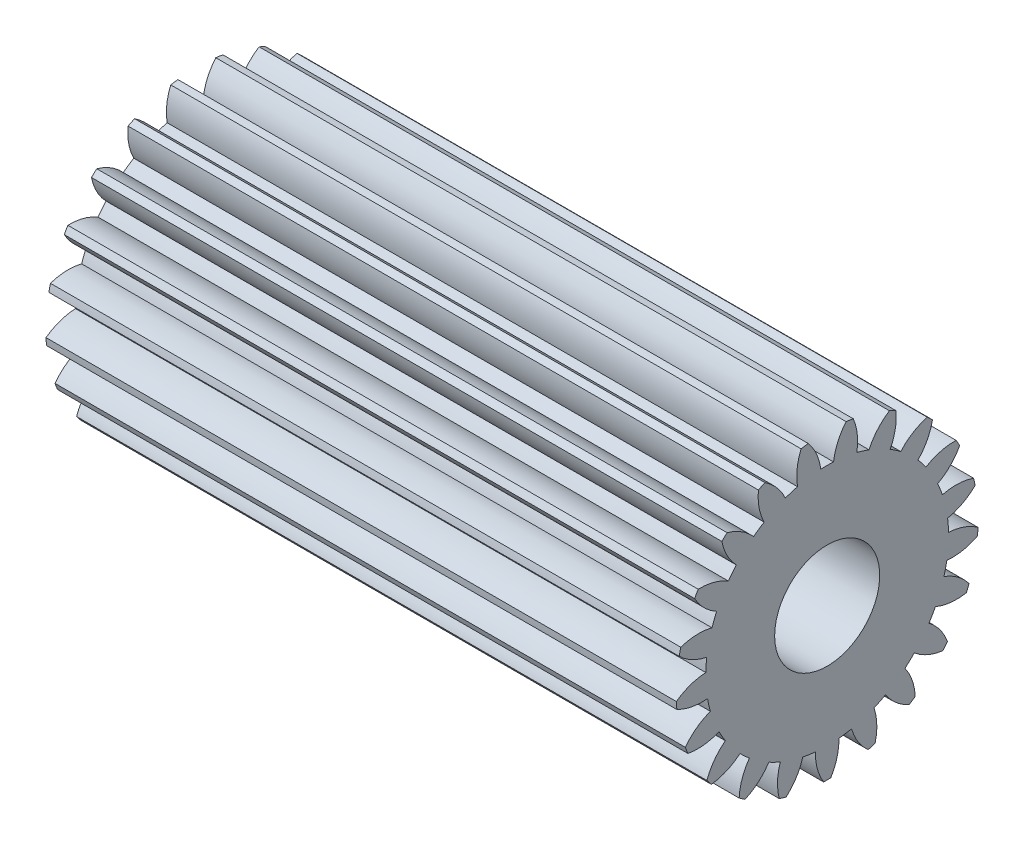
SolidWorks part; units mm, degrees
ref_plane "Plane1" through (0, 0, 0) normal (0, 0, 1) x (1, 0, 0)
ref_plane "Plane2" through (0, 0, 0) normal (0, 1, 0) x (1, 0, 0)
ref_plane "Plane3" through (0, 0, 0) normal (1, 0, 0) x (0, 0, -1)
sketch "HoldingSke" plane through (0, 0, 0) normal (0, 1, 0) x (1, 0, 0)
  line L0 (0, 0) -> (3.7343, -1.4335)
  line L1 (-15, 0) -> (100, 0) construction
  line L2 (0, 0) -> (-2.1039, 2.3779)
  line L3 (0, 0) -> (-11.863, 4.5341)
  line L4 (0, 0) -> (8.0624, 3.0949)
  line L5 (0, 0) -> (-46.8476, -17.4728)
  line L6 (0, 0) -> (-9.9476, -6.7116)
  line L7 (-2.1039, 2.3779) -> (8.6586, 51.2059)
  line L8 (-76.2, 54.61) -> (-75.9, 54.61)
  line L9 (-71.009, 38.7566) -> (-53.1078, 45.2721)
  line L10 (-76.2, 71.12) -> (104.1128, 71.12)
  line L11 (0, 0) -> (-12, 0)
  line L12 (-76.2, 101.6) -> (-76.192, 101.6)
  line L13 (24.9733, 27.94) -> (52.9518, 28.4284)
  line L14 (24.9733, 27.94) -> (24.9743, 27.94)
  line L15 (24.9733, 27.94) -> (100.4006, 29.5858)
  line L16 (-63.627, -0.25) -> (-12.827, -0.25)
  circle A0 centre (0, 0) radius 1
  circle A1 centre (0, 0) radius 2.3115
  circle A2 centre (0, 0) radius 37.5
  circle A3 centre (0, 0) radius 1
  dimension "MHD" = 4.623
  dimension "Hub_dia" = 75
  dimension "Bore" = 2
  dimension "MBD" = 2
  dimension "Num_teeth" = 21
  dimension "Pitch" = 4
  dimension "Overall_len" = 50
  dimension "Show_teeth" = 21
  dimension "Thickness" = 12
  dimension "OAL" = 50.0001
  dimension "T_dim" = 0.3
  dimension "Ap" = 20
  dimension "H" = 19.05
  dimension "Pitch_radius" = 180.3128
  dimension "Width" = 12
  dimension "Backlash" = 0.008
  dimension "Addendum_fac" = 1
  dimension "Dedendum_fac" = 1.25
  dimension "Clearance_fac" = 0.25
  dimension "Dedendum_add" = 0.001
  dimension "Module" = 0.25
sketch "BasProSke" plane through (0, 0, 0) normal (0, 1, 0) x (1, 0, 0)
  line L0 (-10, 0) -> (60, 0) construction
  line L1 (0, 0) -> (0, 2.875)
  line L2 (0, 0) -> (12, 0)
  line L3 (12, 0) -> (12, 2.875)
  line L4 (12, 2.875) -> (0, 2.875)
  dimension "Thickness" = 12
  dimension "Diameter" = 5.75
revolve "Base-Revolve" add sketch "BasProSke" angle 360 about L0
sketch "TooCutSke" plane through (0, 0, 0) normal (1, 0, 0) x (0, 0, -1)
  line L1 (0, 0) -> (0, 107) construction
  line L2 (0, 0) -> (-0.2102, 2.6166) construction
  line L3 (0, 0) -> (-0.7806, 5.1788) construction
  line L4 (-0.2102, 2.6166) -> (-0.3903, 2.5894) construction
  arc A0 (0.1214, 2.3083) -> (-0.1214, 2.3083) centre (0, 0) ccw
  arc A1 (0.3803, 2.8754) -> (-0.3803, 2.8754) centre (0, 0) ccw
  circle A2 centre (0, 0) radius 2.625 construction
  circle A3 centre (0, 0) radius 2.4667 construction
  arc A4 (-0.1214, 2.3083) -> (-0.3803, 2.8754) centre (-1.163, 2.1753) ccw
  arc A5 (0.3803, 2.8754) -> (0.1214, 2.3083) centre (1.163, 2.1753) ccw
  dimension "Root_dia" = 4.623
  dimension "Overcut_dia" = 5.8008
  dimension "Pitch_dia" = 5.25
  dimension "Base_dia" = 4.9334
  dimension "Flank_rad" = 1.05
  dimension "Half_ang" = 8.571
  dimension "Half_CT" = 0.1822
extrude "ToothCut" cut sketch "TooCutSke" along normal through all
fillet "Breaks" [suppressed] radius 0.005
fillet "RootFillets" [suppressed] radius 0.0635
pattern_circular "TeethCuts" count 21 every 17.143 about axis through (-10, 0, 0) along (1, 0, 0) of "ToothCut", "RootFillets", "Breaks"
sketch "HubNeaOneSke" plane through (0, 0, 0) normal (-1, 0, 0) x (0, 0, 1)
  circle A0 centre (0, 0) radius 2.3115
  dimension "Diameter" = 4.623
extrude "HubNearOne" [suppressed] add sketch "HubNeaOneSke" along normal blind 38.0001
sketch "HubNeaBotSke" plane through (0, 0, 0) normal (-1, 0, 0) x (0, 0, 1)
  circle A0 centre (0, 0) radius 2.3115
  dimension "Diameter" = 4.623
extrude "HubNearBoth" [suppressed] add sketch "HubNeaBotSke" along normal blind 19
ref_plane "FarPln" through (12, 0, 0) normal (1, 0, 0) x (0, 0, -1)
sketch "HubFarSke" plane through (12, 0, 0) normal (1, 0, 0) x (0, 0, -1)
  circle A0 centre (0, 0) radius 2.3115
  dimension "Diameter" = 4.623
extrude "HubFar" [suppressed] add sketch "HubFarSke" along normal blind 19
sketch "BorSke" plane through (0, 0, 0) normal (1, 0, 0) x (0, 0, -1)
  circle A0 centre (0, 0) radius 1
  dimension "Diameter" = 2
extrude "Bore" cut sketch "BorSke" along normal mid plane 100.0001
sketch "KeySke" plane through (0, 0, 0) normal (1, 0, 0) x (0, 0, -1)
  line L0 (-0.4, 0) -> (-0.4, 1.3)
  line L1 (-0.4, 1.3) -> (0.4, 1.3)
  line L2 (0.4, 1.3) -> (0.4, 0)
  line L3 (0, 0) -> (0, 34) construction
  line L4 (-0.4, 0) -> (0.4, 0)
  dimension "Offset" = 1.3
  dimension "Width" = 0.8
extrude "Keyway" [suppressed] cut sketch "KeySke" along normal mid plane 100.0001
pattern_circular "Keyway2" [suppressed] count 2 every 90 about axis through (-10, 0, 0) along (1, 0, 0)
equation "' \"Module@HoldingSke\" = 6.35"
equation "' \"Num_teeth@HoldingSke\" = 12"
equation "' \"Ap@HoldingSke\" =  20"
equation "' \"Ap@HoldingSke\" = 20"
equation "' \"Width@HoldingSke\" = 0.5 * 25.4"
equation "' \"Hub_dia@HoldingSke\"= 1 * 25.4"
equation "' \"Hub_dia@HoldingSke\" = 1 * 25.4"
equation "' \"Overall_len@HoldingSke\" = 1.0 * 25.4"
equation "' \"Bore@HoldingSke\" = 0.75 * 25.4"
equation "' \"T_dim@HoldingSke\" = 0.1 * 25.4"
equation "' \"Width@KeySke\" = 0.25 * 25.4"
equation "' \"Show_teeth@HoldingSke\" = 13"
equation "' \"Backlash@HoldingSke\" = 0.009 * 25.4"
equation "' \"Addendum_fac@HoldingSke\" = 1.0"
equation "' \"Dedendum_fac@HoldingSke\" = 1.25"
equation "' \"Dedendum_add@HoldingSke\" = 0.00005 * 25.4"
equation "' \"Clearance_fac@HoldingSke\" = 0.25"
equation "\"Pitch@HoldingSke\" = 1 / \"Module@HoldingSke\""
equation "\"Overcut_dia@TooCutSke\" = (\"Num_teeth@HoldingSke\" + 2 * \"Addendum_fac@HoldingSke\") / \"Pitch@HoldingSke\" + 0.002 * 25.4"
equation "\"Pitch_dia@TooCutSke\" = \"Num_teeth@HoldingSke\" / \"Pitch@HoldingSke\""
equation "\"Base_dia@TooCutSke\" = \"Num_teeth@HoldingSke\" / \"Pitch@HoldingSke\" * cos((\"Ap@HoldingSke\"  * 3.14159265 / 180))"
equation "\"Root_dia@TooCutSke\" = (\"Num_teeth@HoldingSke\" + 2) / \"Pitch@HoldingSke\" - 2 * (\"Addendum_fac@HoldingSke\" + \"Dedendum_fac@HoldingSke\") / \"Pitch@HoldingSke\" - \"Dedendum_add@HoldingSke\" * 2"
equation "\"Half_ang@TooCutSke\" = 180 / \"Num_teeth@HoldingSke\""
equation "\"Half_CT@TooCutSke\" = \"Num_teeth@HoldingSke\" / \"Pitch@HoldingSke\" * sin((3.14159265 / 2 / \"Num_teeth@HoldingSke\")) / 2 - 7 * \"Backlash@HoldingSke\" / 4"
equation "\"Flank_rad@TooCutSke\" = \"Num_teeth@HoldingSke\" / \"Pitch@HoldingSke\" / 5"
equation "\"Radius@RootFillets\" = \"Clearance_fac@HoldingSke\" / \"Pitch@HoldingSke\" + \"Dedendum_add@HoldingSke\""
equation "\"Break_rad@Breaks\" = 0.02 / \"Pitch@HoldingSke\""
equation "\"Thickness@HoldingSke\" = \"Width@HoldingSke\""
equation "\"OAL@HoldingSke\" = \"Thickness@HoldingSke\""
equation "\"MHD@HoldingSke\" = (\"Num_teeth@HoldingSke\" + 2) / \"Pitch@HoldingSke\" - 2 * (\"Addendum_fac@HoldingSke\" + \"Dedendum_fac@HoldingSke\")  / \"Pitch@HoldingSke\" - \"Dedendum_add@HoldingSke\" * 2"
equation "\"MBD@HoldingSke\" = (\"Num_teeth@HoldingSke\" + 2) / \"Pitch@HoldingSke\" - 2 * (\"Addendum_fac@HoldingSke\" + \"Dedendum_fac@HoldingSke\")  / \"Pitch@HoldingSke\" - \"Dedendum_add@HoldingSke\" * 2 - 0.002 * 25.4"
equation "\"MHD@HoldingSke\" = ((sgn( \"MHD@HoldingSke\" - \"Hub_dia@HoldingSke\" )-1)*( \"MHD@HoldingSke\" - \"Hub_dia@HoldingSke\" ))/-2+ \"Hub_dia@HoldingSke\""
equation "\"MBD@HoldingSke\" = ((sgn( \"MBD@HoldingSke\" - \"Bore@HoldingSke\" )-1)*( \"MBD@HoldingSke\" - \"Bore@HoldingSke\" ))/-2+ \"Bore@HoldingSke\""
equation "\"OAL@HoldingSke\" = ((sgn( \"OAL@HoldingSke\" - \"Overall_len@HoldingSke\" )+1)*( \"OAL@HoldingSke\" - \"Overall_len@HoldingSke\" ))/2 + \"Overall_len@HoldingSke\" + 0.000002 * 25.4"
equation "\"Num_teeth@TeethCuts\" = int( \"Show_teeth@HoldingSke\" ) + 1"
equation "\"Num_teeth@TeethCuts\" = ((sgn( \"Num_teeth@TeethCuts\" - \"Num_teeth@HoldingSke\" )-1)*( \"Num_teeth@TeethCuts\" - \"Num_teeth@HoldingSke\" ))/-2+ \"Num_teeth@HoldingSke\""
equation "\"Num_teeth@TeethCuts\" = ((sgn( \"Num_teeth@TeethCuts\" - 2.0)+1)*( \"Num_teeth@TeethCuts\" - 2.0))/2 +2.0"
equation "\"Angle@TeethCuts\" = 360.0 / \"Num_teeth@HoldingSke\""
equation "\"Diameter@BasProSke\" = (\"Num_teeth@HoldingSke\" + 2 * \"Addendum_fac@HoldingSke\") / \"Pitch@HoldingSke\""
equation "\"Thickness@BasProSke\"  = \"Thickness@HoldingSke\""
equation "' \"Fillet_rad@BasProSke\" =  \"Thickness@HoldingSke\" * 0.05"
equation "' \"Fillet_rad@BasProSke\" = \"Thickness@HoldingSke\" * 0.05"
equation "\"MHD@HoldingSke\" = ((sgn( \"MHD@HoldingSke\" - \"Root_dia@TooCutSke\" )-1)*( \"MHD@HoldingSke\" - \"Root_dia@TooCutSke\" ))/-2+ \"Root_dia@TooCutSke\""
equation "\"Diameter@HubNeaOneSke\" = \"MHD@HoldingSke\""
equation "\"Length@HubNearOne\" = \"OAL@HoldingSke\" - \"Thickness@BasProSke\""
equation "\"Diameter@HubNeaBotSke\" = \"MHD@HoldingSke\""
equation "\"Length@HubNearBoth\" = ( \"OAL@HoldingSke\" - \"Thickness@BasProSke\" ) / 2.0"
equation "\"Thickness@FarPln\" = \"Thickness@BasProSke\""
equation "\"Diameter@HubFarSke\" = \"MHD@HoldingSke\""
equation "\"Length@HubFar\" = ( \"OAL@HoldingSke\" - \"Thickness@BasProSke\" ) / 2.0"
equation "\"Diameter@BorSke\" = \"MBD@HoldingSke\""
equation "\"D1@Bore\" = \"OAL@HoldingSke\" * 2.0"
equation "\"D1@Keyway\" = \"OAL@HoldingSke\" * 2.0"
equation "\"Offset@KeySke\" = \"T_dim@HoldingSke\" + \"MBD@HoldingSke\" / 2.0"
